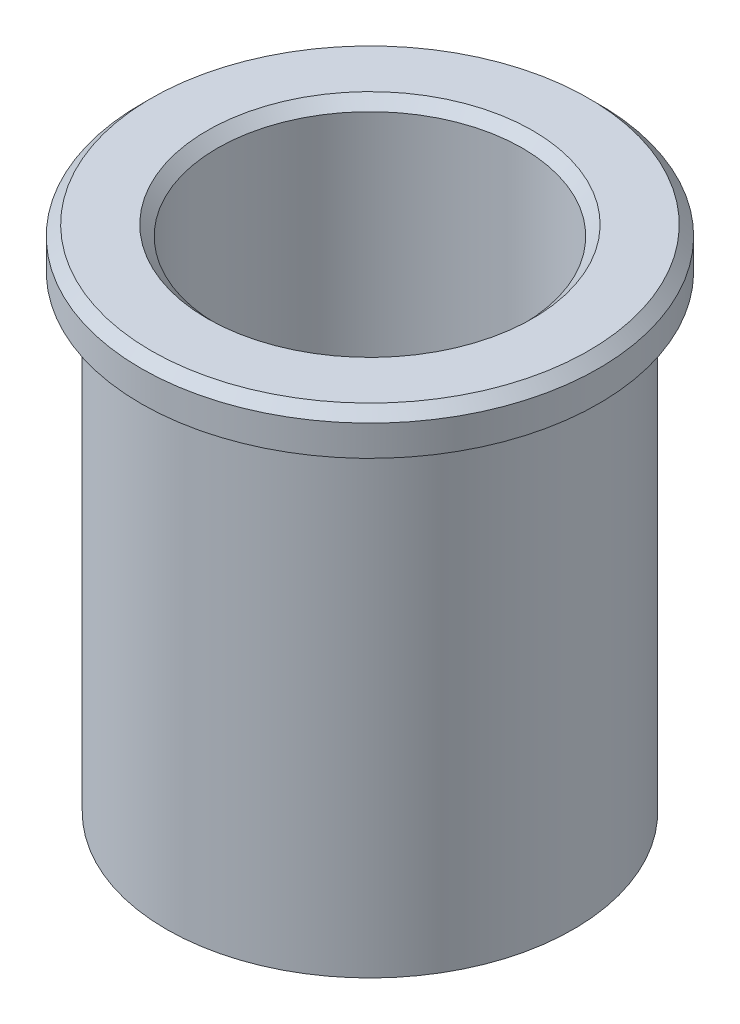
SolidWorks part; units mm, degrees
ref_plane "Plan de face" through (0, 0, 0) normal (0, 0, 1) x (1, 0, 0)
ref_plane "Plan de dessus" through (0, 0, 0) normal (0, 1, 0) x (1, 0, 0)
ref_plane "Plan de droite" through (0, 0, 0) normal (1, 0, 0) x (0, 0, -1)
sketch "Esquisse1" plane through (0, 0, 0) normal (0, 0, 1) x (1, 0, 0)
  line L0 (16, 0) -> (21.5, 0)
  line L1 (22.5, -1) -> (22.5, -4)
  line L2 (22.5, -4) -> (20, -4)
  line L3 (20, -4) -> (20, -50)
  line L4 (20, -50) -> (16, -50)
  line L5 (15, -49) -> (15, -1)
  line L6 (0, 22.6164) -> (0, -72.0247) construction
  line L7 (21.5, 0) -> (22.5, -1)
  line L8 (15, -1) -> (16, 0)
  line L9 (16, -50) -> (15, -49)
  point P0 (15, 0)
  point P1 (22.5, 0)
  point P7 (15, -50)
  dimension "D1" = 30
  dimension "D2" = 40
  dimension "D3" = 45
  dimension "D4" = 4
  dimension "D5" = 50
revolve "Révolution1" add sketch "Esquisse1" angle 360 about L6
